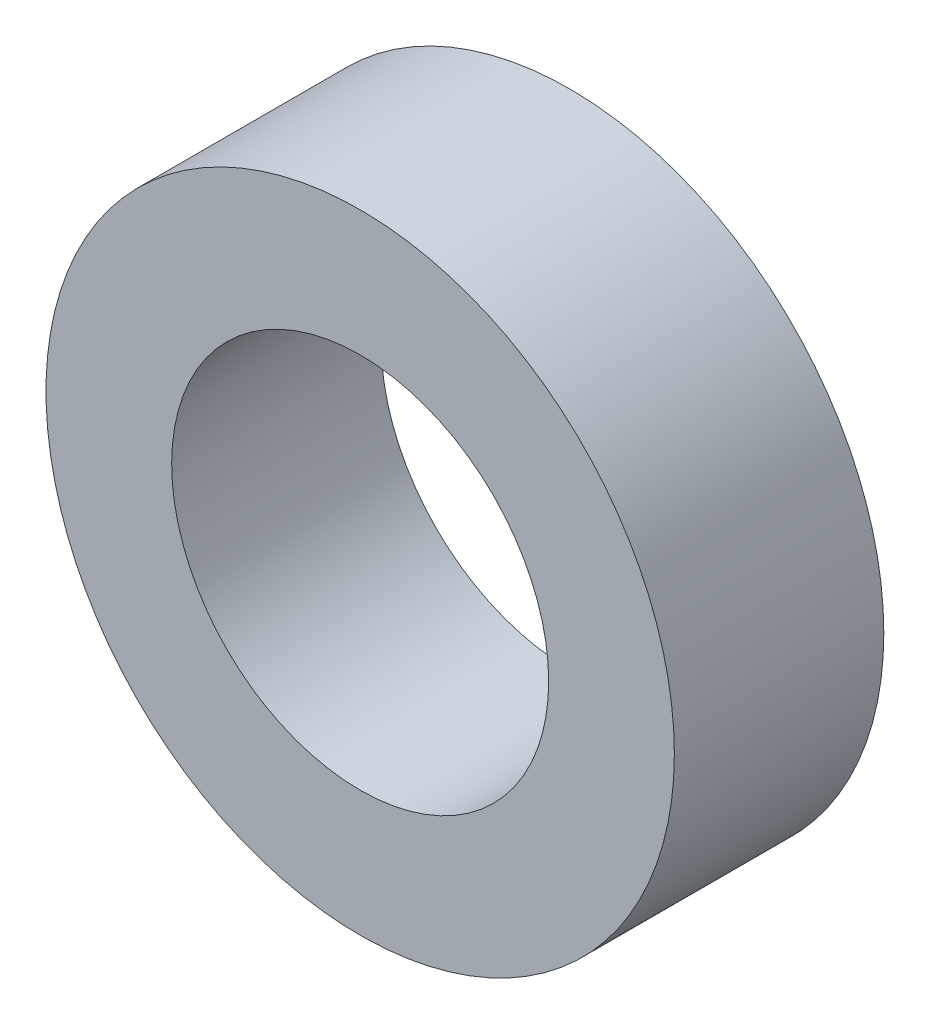
SolidWorks part; units mm, degrees
ref_plane "Front Plane" through (0, 0, 0) normal (0, 0, 1) x (1, 0, 0)
ref_plane "Top Plane" through (0, 0, 0) normal (0, 1, 0) x (1, 0, 0)
ref_plane "Right Plane" through (0, 0, 0) normal (1, 0, 0) x (0, 0, -1)
sketch "Sketch1" plane through (0, 0, 0) normal (0, 0, 1) x (1, 0, 0)
  circle A0 centre (0, 0) radius 15
  circle A1 centre (0, 0) radius 9
  dimension "D1" = 18
  dimension "D2" = 30
extrude "Boss-Extrude1" add sketch "Sketch1" along normal mid plane 10
